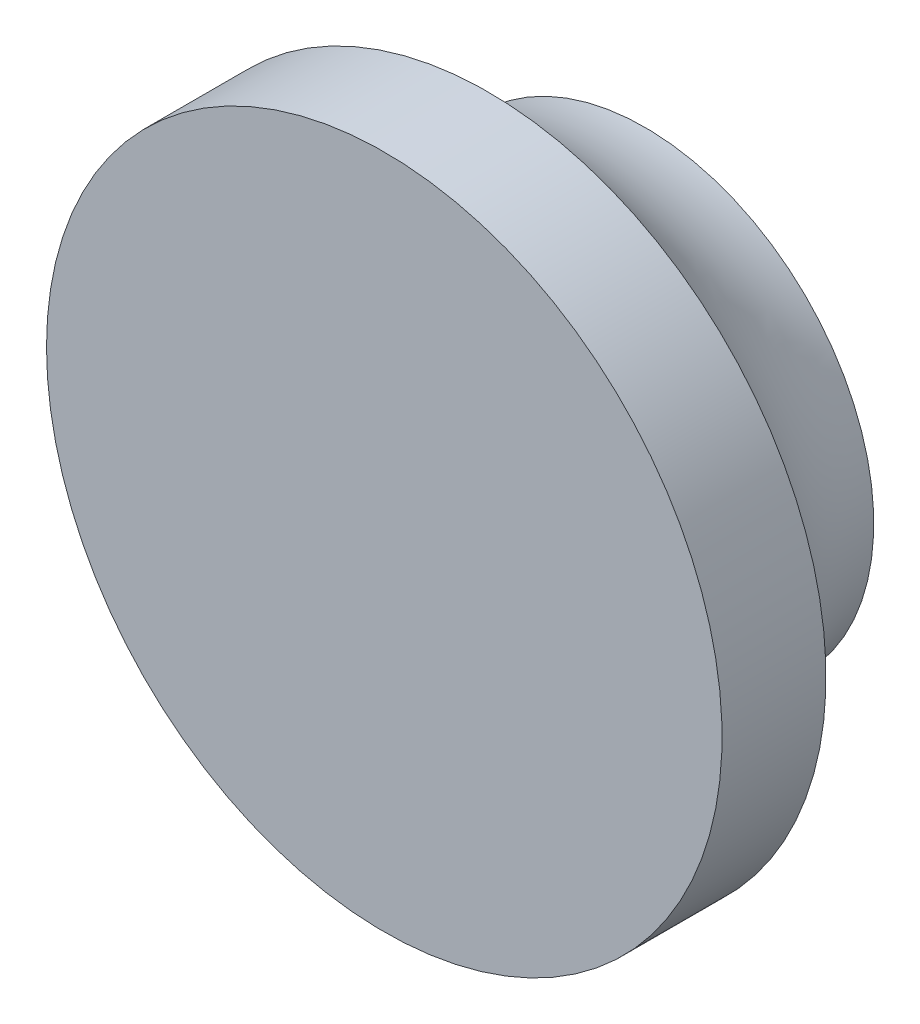
SolidWorks part; units mm, degrees
ref_plane "Front Plane" through (0, 0, 0) normal (0, 0, 1) x (1, 0, 0)
ref_plane "Top Plane" through (0, 0, 0) normal (0, 1, 0) x (1, 0, 0)
ref_plane "Right Plane" through (0, 0, 0) normal (1, 0, 0) x (0, 0, -1)
ref_plane "Plane1" through (206.3396, 0, 0) normal (-1, 0, 0) x (0, 0, 1)
sketch "Sketch4" plane through (206.3396, 0, 0) normal (-1, 0, 0) x (0, 0, 1)
  line L0 (280.7728, -95.8968) -> (309.4841, -95.8968) construction
  line L1 (296.832, -82.8968) -> (296.832, -95.8968) construction
  line L2 (286.7935, -95.8968) -> (296.832, -95.8968) construction
  line L3 (286.7935, -87.0968) -> (286.7935, -95.8968) construction
  line L4 (296.832, -82.8968) -> (292.832, -82.8968) construction
  line L5 (276.1644, -95.8968) -> (318.4438, -95.8968)
  line L6 (296.832, -82.8968) -> (296.832, -95.8968)
  line L7 (286.7935, -95.8968) -> (296.832, -95.8968)
  line L8 (286.7935, -87.0968) -> (286.7935, -95.8968)
  line L9 (296.832, -82.8968) -> (292.832, -82.8968)
  arc A0 (286.7935, -87.0968) -> (292.832, -82.8968) centre (286.4118, -80.1072) ccw construction
  arc A1 (286.7935, -87.0968) -> (292.832, -82.8968) centre (286.4118, -80.1072) ccw
  point P5 (276.1644, -95.8968)
  point P9 (318.4438, -95.8968)
revolve "Revolve1" add sketch "Sketch4" angle 360 about L5
